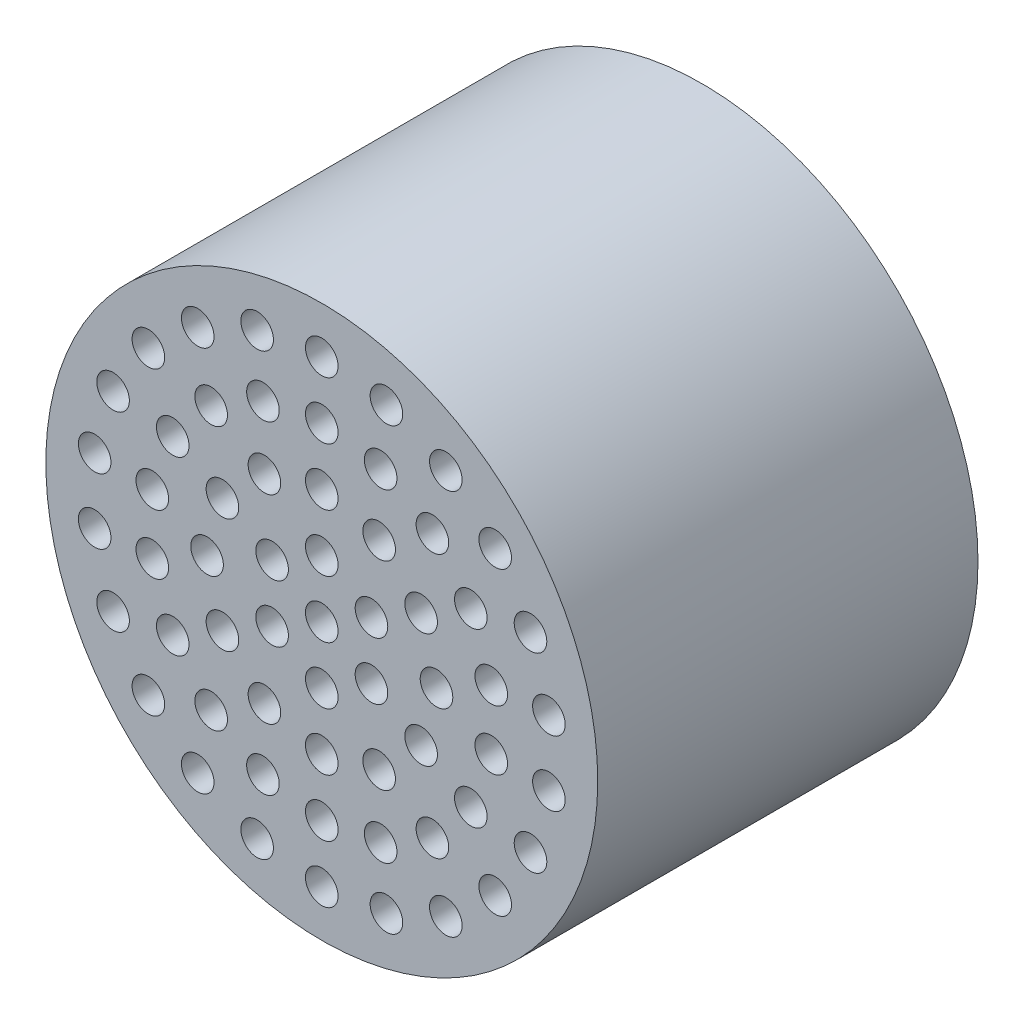
SolidWorks part; units mm, degrees
material "PBT à usage général"
ref_plane "Plan de face" through (0, 0, 0) normal (0, 0, 1) x (1, 0, 0)
ref_plane "Plan de dessus" through (0, 0, 0) normal (0, 1, 0) x (1, 0, 0)
ref_plane "Plan de droite" through (0, 0, 0) normal (1, 0, 0) x (0, 0, -1)
sketch "Esquisse1" plane through (0, 0, 0) normal (0, 0, 1) x (1, 0, 0)
  circle A0 centre (16.6252, 7.1087) radius 25.4
  dimension "D1" = 50.8
extrude "Boss.-Extru.1" add sketch "Esquisse1" along normal blind 25
sketch "Esquisse6" plane through (0, 0, 0) normal (0, 0, -1) x (-1, 0, 0)
  line L0 (-42.0252, 7.1087) -> (8.7748, 7.1087) construction
  circle A0 centre (-16.6252, 7.1087) radius 25.4 construction
  circle A1 centre (-39.5252, 7.1087) radius 1.55
  circle A2 centre (6.2748, 7.1087) radius 1.55
  point P12 (-16.6252, 7.1087)
  dimension "D1" = 3.1
  dimension "D2" = 2.5
  dimension "D3" = 2
extrude "Enlèv. mat.-Extru.4" cut sketch "Esquisse6" against normal blind 11
sketch "Esquisse8" plane through (0, 0, 25) normal (0, 0, 1) x (1, 0, 0)
  line L0 (-8.7748, 7.1087) -> (16.6252, 7.1087) construction
  circle A0 centre (16.6252, 7.1087) radius 25.4 construction
  circle A1 centre (16.6252, 7.1087) radius 25.4
  dimension "D1" = 50.8
extrude "Boss.-Extru.3" add sketch "Esquisse8" along normal blind 10
sketch "Esquisse9" plane through (0, 0, 35) normal (0, 0, 1) x (1, 0, 0)
  line L0 (16.6252, 32.5087) -> (16.6252, 7.1087) construction
  circle A0 centre (16.6252, 7.1087) radius 25.4 construction
  circle A1 centre (16.6252, 7.1087) radius 1.5
  circle A2 centre (16.6252, 12.3887) radius 1.5
  circle A3 centre (21.1978, 9.7487) radius 1.5
  circle A4 centre (21.1978, 4.4687) radius 1.5
  circle A5 centre (16.6252, 1.8287) radius 1.5
  circle A6 centre (12.0526, 4.4687) radius 1.5
  circle A7 centre (12.0526, 9.7487) radius 1.5
  circle A8 centre (16.6252, 17.6687) radius 1.5
  circle A9 centre (21.9052, 16.2539) radius 1.5
  circle A10 centre (25.7704, 12.3887) radius 1.5
  circle A11 centre (27.1852, 7.1087) radius 1.5
  circle A12 centre (25.7704, 1.8287) radius 1.5
  circle A13 centre (21.9052, -2.0365) radius 1.5
  circle A14 centre (16.6252, -3.4513) radius 1.5
  circle A15 centre (11.3452, -2.0365) radius 1.5
  circle A16 centre (7.48, 1.8287) radius 1.5
  circle A17 centre (6.0652, 7.1087) radius 1.5
  circle A18 centre (7.48, 12.3887) radius 1.5
  circle A19 centre (11.3452, 16.2539) radius 1.5
  circle A20 centre (16.6252, 22.9487) radius 1.5
  circle A21 centre (22.0428, 21.9934) radius 1.5
  circle A22 centre (26.807, 19.2429) radius 1.5
  circle A23 centre (30.3431, 15.0287) radius 1.5
  circle A24 centre (32.2246, 9.8593) radius 1.5
  circle A25 centre (32.2246, 4.3581) radius 1.5
  circle A26 centre (30.3431, -0.8113) radius 1.5
  circle A27 centre (26.807, -5.0254) radius 1.5
  circle A28 centre (22.0428, -7.776) radius 1.5
  circle A29 centre (16.6252, -8.7313) radius 1.5
  circle A30 centre (11.2076, -7.776) radius 1.5
  circle A31 centre (6.4435, -5.0254) radius 1.5
  circle A32 centre (2.9074, -0.8113) radius 1.5
  circle A33 centre (1.0259, 4.3581) radius 1.5
  circle A34 centre (1.0259, 9.8593) radius 1.5
  circle A35 centre (2.9074, 15.0287) radius 1.5
  circle A36 centre (6.4435, 19.2429) radius 1.5
  circle A37 centre (11.2076, 21.9934) radius 1.5
  circle A38 centre (16.6252, 28.2287) radius 1.5
  circle A39 centre (22.5754, 27.3732) radius 1.5
  circle A40 centre (28.0435, 24.876) radius 1.5
  circle A41 centre (32.5866, 20.9394) radius 1.5
  circle A42 centre (35.8366, 15.8823) radius 1.5
  circle A43 centre (37.5302, 10.1144) radius 1.5
  circle A44 centre (37.5302, 4.103) radius 1.5
  circle A45 centre (35.8366, -1.6649) radius 1.5
  circle A46 centre (32.5866, -6.7219) radius 1.5
  circle A47 centre (28.0435, -10.6586) radius 1.5
  circle A48 centre (22.5754, -13.1558) radius 1.5
  circle A49 centre (16.6252, -14.0113) radius 1.5
  circle A50 centre (10.675, -13.1558) radius 1.5
  circle A51 centre (5.2069, -10.6586) radius 1.5
  circle A52 centre (0.6638, -6.7219) radius 1.5
  circle A53 centre (-2.5862, -1.6649) radius 1.5
  circle A54 centre (-4.2798, 4.103) radius 1.5
  circle A55 centre (-4.2798, 10.1144) radius 1.5
  circle A56 centre (-2.5862, 15.8823) radius 1.5
  circle A57 centre (0.6638, 20.9394) radius 1.5
  circle A58 centre (5.2069, 24.876) radius 1.5
  circle A59 centre (10.675, 27.3732) radius 1.5
  point P21 (16.6252, 7.1087)
  point P45 (16.6252, 7.1087)
  point P82 (16.6252, 7.1087)
  point P127 (16.6252, 7.1087)
  dimension "D1" = 3
  dimension "D2" = 5.28
  dimension "D6" = 15.84
  dimension "D4" = 10.56
  dimension "D8" = 21.12
  dimension "D3" = 6
  dimension "D5" = 12
  dimension "D7" = 18
  dimension "D9" = 22
extrude "Enlèv. mat.-Extru.5" cut sketch "Esquisse9" against normal blind 10
sketch "Esquisse10" plane through (0, 0, 35) normal (0, 0, 1) x (1, 0, 0)
  line L0 (0, 7.1087) -> (16.6252, 7.1087) construction
  line L1 (0, -17.9722) -> (0, 17.9722) construction
ref_plane "Plan1" through (16.6252, 0, 0) normal (1, 0, 0) x (0, 0, -1)
sketch "Esquisse12" plane through (16.6252, 0, 0) normal (1, 0, 0) x (0, 0, -1)
  line L0 (-35, 32.5087) -> (-35, 7.1087) construction
  line L1 (-35, 32.5087) -> (-35, -18.2913) construction
  line L2 (-35, 7.1087) -> (0, 7.1087) construction
  line L3 (0, 27.94) -> (0, -27.94) construction
  line L4 (0, 7.1087) -> (0, 27.1087)
  line L5 (0, 27.1087) -> (-25, 30.1087)
  line L6 (-25, 30.1087) -> (-25, 7.1087)
  line L7 (-25, 7.1087) -> (0, 7.1087)
  dimension "D1" = 23
  dimension "D2" = 20
  dimension "D3" = 10
revolve "Enlèvement de matière-Révolution1" cut sketch "Esquisse12" angle 360 about L7
